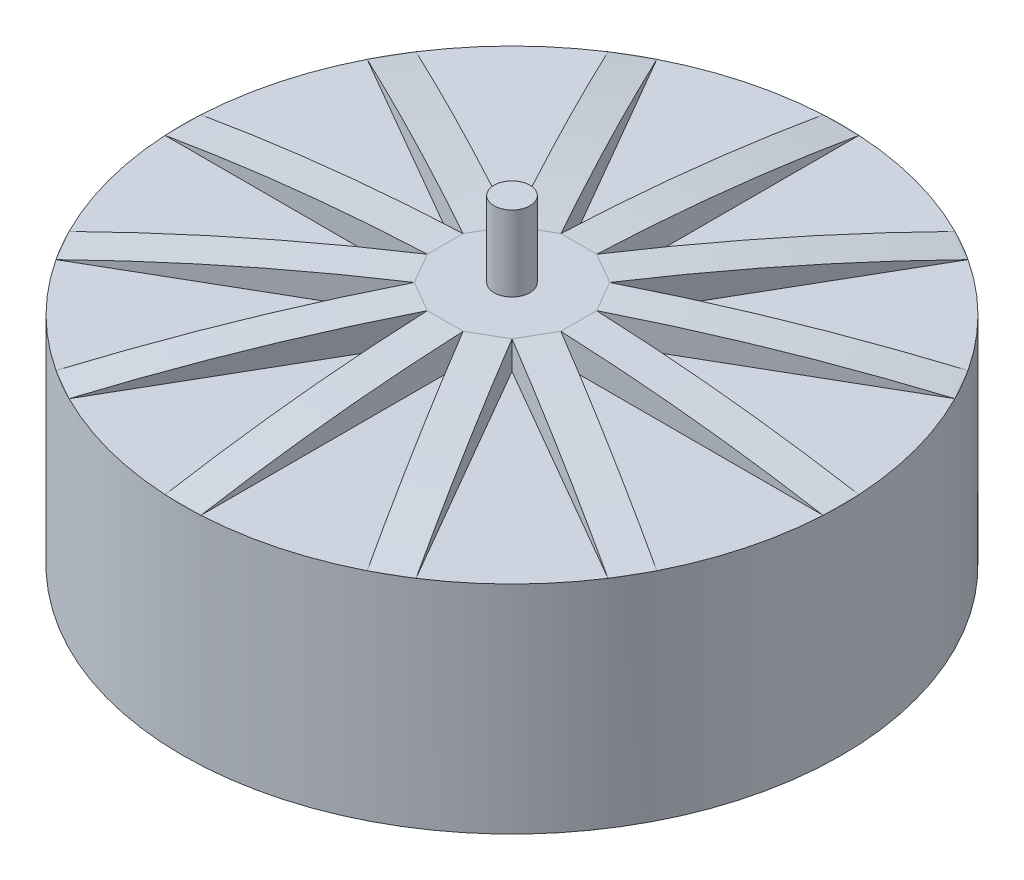
SolidWorks part; units mm, degrees
ref_plane "Спереди" through (0, 0, 0) normal (0, 0, 1) x (1, 0, 0)
ref_plane "Сверху" through (0, 0, 0) normal (0, 1, 0) x (1, 0, 0)
ref_plane "Справа" through (0, 0, 0) normal (1, 0, 0) x (0, 0, -1)
sketch "Эскиз1" plane through (0, 0, 0) normal (0, 1, 0) x (1, 0, 0)
  circle A0 centre (0, 0) radius 35
extrude "Бобышка-Вытянуть1" add sketch "Эскиз1" along normal blind 23
sketch "Эскиз2" plane through (0, 23, 0) normal (0, 1, 0) x (1, 0, 0)
  circle A0 centre (0, 0) radius 1.9
extrude "Бобышка-Вытянуть2" add sketch "Эскиз2" along normal blind 11
sketch "Эскиз4" plane through (0, 23, 0) normal (0, 1, 0) x (1, 0, 0)
  line L0 (-1.6454, 0.95) -> (-19.1196, -29.3162)
  line L1 (-1.9, 0) -> (1.9, 0)
  line L2 (-1.9, 0) -> (-1.9, -34.9484)
  line L3 (-1.9, -34.9484) -> (1.9, -34.9484)
  line L4 (1.9, 0) -> (1.9, -34.9484)
  line L5 (-1.9, 0) -> (1.9, -34.9484) construction
  line L6 (-1.9, -34.9484) -> (1.9, 0) construction
  line L7 (1.6454, -0.95) -> (-15.8287, -31.2162)
  line L8 (-19.1196, -29.3162) -> (-15.8287, -31.2162)
  line L9 (-1.6454, 0.95) -> (1.6454, -0.95)
  line L10 (-0.95, 1.6454) -> (-31.2162, -15.8287)
  line L11 (0.95, -1.6454) -> (-29.3162, -19.1196)
  line L12 (-31.2162, -15.8287) -> (-29.3162, -19.1196)
  line L13 (-0.95, 1.6454) -> (0.95, -1.6454)
  line L14 (0, 1.9) -> (-34.9484, 1.9)
  line L15 (0, -1.9) -> (-34.9484, -1.9)
  line L16 (-34.9484, 1.9) -> (-34.9484, -1.9)
  line L17 (0, 1.9) -> (0, -1.9)
  line L18 (0.95, 1.6454) -> (-29.3162, 19.1196)
  line L19 (-0.95, -1.6454) -> (-31.2162, 15.8287)
  line L20 (-29.3162, 19.1196) -> (-31.2162, 15.8287)
  line L21 (0.95, 1.6454) -> (-0.95, -1.6454)
  line L22 (1.6454, 0.95) -> (-15.8287, 31.2162)
  line L23 (-1.6454, -0.95) -> (-19.1196, 29.3162)
  line L24 (-15.8287, 31.2162) -> (-19.1196, 29.3162)
  line L25 (1.6454, 0.95) -> (-1.6454, -0.95)
  line L26 (1.9, 0) -> (1.9, 34.9484)
  line L27 (-1.9, 0) -> (-1.9, 34.9484)
  line L28 (1.9, 34.9484) -> (-1.9, 34.9484)
  line L29 (1.9, 0) -> (-1.9, 0)
  line L30 (1.6454, -0.95) -> (19.1196, 29.3162)
  line L31 (-1.6454, 0.95) -> (15.8287, 31.2162)
  line L32 (19.1196, 29.3162) -> (15.8287, 31.2162)
  line L33 (1.6454, -0.95) -> (-1.6454, 0.95)
  line L34 (0.95, -1.6454) -> (31.2162, 15.8287)
  line L35 (-0.95, 1.6454) -> (29.3162, 19.1196)
  line L36 (31.2162, 15.8287) -> (29.3162, 19.1196)
  line L37 (0.95, -1.6454) -> (-0.95, 1.6454)
  line L38 (0, -1.9) -> (34.9484, -1.9)
  line L39 (0, 1.9) -> (34.9484, 1.9)
  line L40 (34.9484, -1.9) -> (34.9484, 1.9)
  line L41 (0, -1.9) -> (0, 1.9)
  line L42 (-0.95, -1.6454) -> (29.3162, -19.1196)
  line L43 (0.95, 1.6454) -> (31.2162, -15.8287)
  line L44 (29.3162, -19.1196) -> (31.2162, -15.8287)
  line L45 (-0.95, -1.6454) -> (0.95, 1.6454)
  line L46 (-1.6454, -0.95) -> (15.8287, -31.2162)
  line L47 (1.6454, 0.95) -> (19.1196, -29.3162)
  line L48 (15.8287, -31.2162) -> (19.1196, -29.3162)
  line L49 (-1.6454, -0.95) -> (1.6454, 0.95)
  circle A0 centre (0, 0) radius 1.9 construction
  circle A1 centre (0, 0) radius 1.9 construction
  circle A2 centre (0, 0) radius 35 construction
  point P4 (0, -17.4742)
  point P58 (0, 0)
  dimension "D1" = 12
extrude "Бобышка-Вытянуть6" add sketch "Эскиз4" along normal blind 3 contours L27 L28 L26 L29
sketch "Эскиз8" plane through (0, 34, 0) normal (0, 1, 0) x (1, 0, 0)
  line L0 (0, 1.9) -> (0, -1.9) construction
  line L1 (0, -1.9) -> (-1.9, 0) construction
  line L2 (-1.9, 0) -> (1.9, 0) construction
  line L3 (0.95, 1.6454) -> (-0.95, -1.6454) construction
  line L4 (1.6454, 0.95) -> (-1.6454, -0.95) construction
  line L5 (1.9, 0) -> (-1.9, 0) construction
  line L6 (1.6454, -0.95) -> (-1.6454, 0.95) construction
  line L7 (0.95, -1.6454) -> (-0.95, 1.6454) construction
  line L8 (0, -1.9) -> (0, 1.9) construction
  line L9 (-0.95, -1.6454) -> (0.95, 1.6454) construction
  line L10 (-1.6454, -0.95) -> (1.6454, 0.95) construction
  line L11 (-1.9, 0) -> (1.9, 0) construction
  line L12 (-1.6454, 0.95) -> (1.6454, -0.95) construction
  line L13 (-0.95, 1.6454) -> (0.95, -1.6454) construction
  circle A0 centre (0, 0) radius 1.9 construction
  point P32 (0, 0)
  dimension "D1" = 12
pattern_circular "Круговой массив1" count 12 over 360 about axis through (0, 0, 0) along (0, 1, 0) of "Бобышка-Вытянуть6"
sketch "Эскиз12" plane through (-0.95, 0, 1.6454) normal (-0.5, 0, 0.866) x (0.866, 0, 0.5)
  line L0 (-34.9484, 26) -> (-20.9484, 26) construction
  line L1 (-7.0909, 26) -> (-34.9484, 26) construction
  line L2 (-20.9484, 26) -> (-20.9484, 24.9572) construction
  line L3 (-34.9484, 23) -> (-7.0909, 23)
  line L4 (-7.0909, 23) -> (-7.0909, 26)
  line L5 (-34.9484, 23) -> (-34.9484, 26)
  line L6 (-34.9484, 26) -> (-7.0909, 26)
  spline S0 degree 2 poles (-34.9484, 23) (-21.1151, 25.3888) (-7.0909, 26) knots 0 0 0 1 1 1
  line M5 (-7.0909, 26) -> (-34.9484, 26)
  line M6 (-34.9484, 26) -> (-34.9484, 23)
extrude "Вырез-Вытянуть3" cut sketch "Эскиз12" against normal blind 4 contours S0 M6 M5
pattern_circular "Круговой массив2" count 12 over 360 of "Вырез-Вытянуть3"
